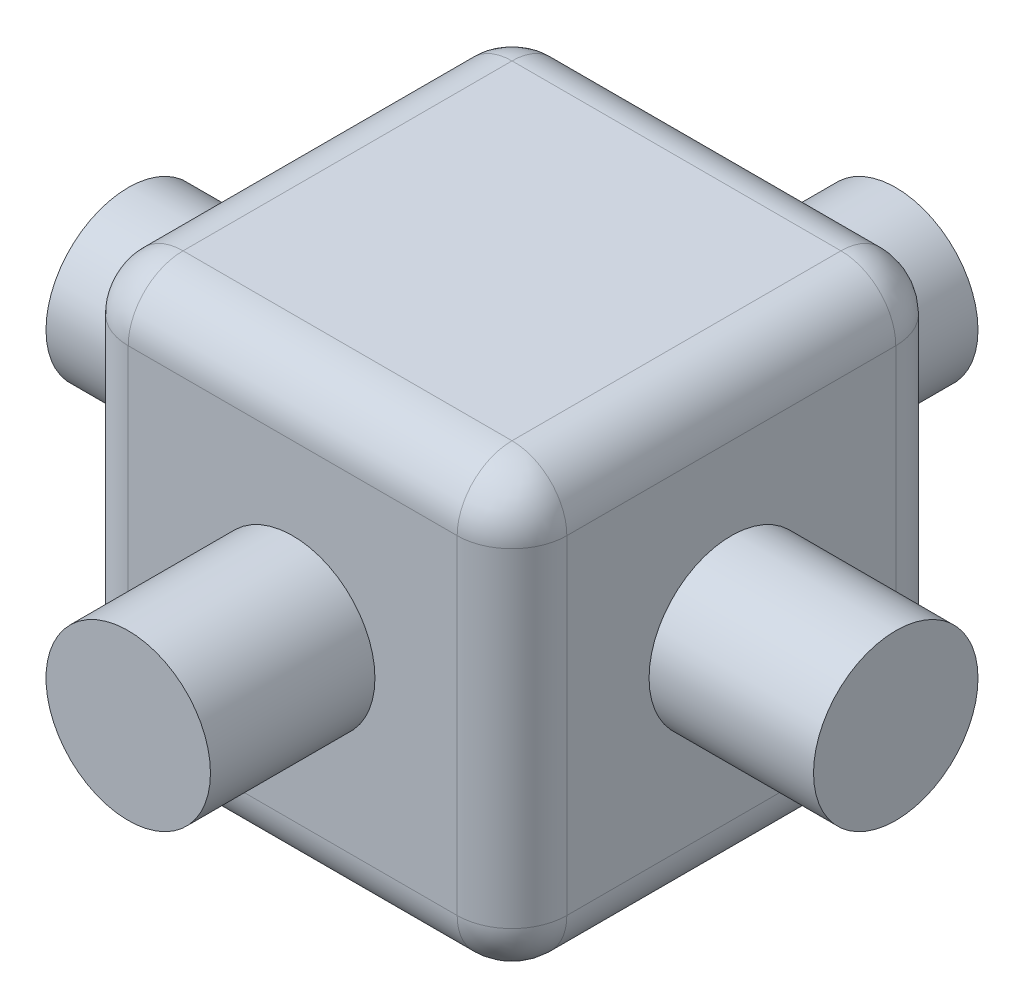
SolidWorks part; units mm, degrees
ref_plane "Front Plane" through (0, 0, 0) normal (0, 0, 1) x (1, 0, 0)
ref_plane "Top Plane" through (0, 0, 0) normal (0, 1, 0) x (1, 0, 0)
ref_plane "Right Plane" through (0, 0, 0) normal (1, 0, 0) x (0, 0, -1)
sketch "Sketch1" plane through (0, 0, 0) normal (0, 0, 1) x (1, 0, 0)
  circle A0 centre (0, 0) radius 0.75
  dimension "D1" = 1.5
extrude "Boss-Extrude1" add sketch "Sketch1" along normal mid plane 7
ref_axis "Axis1" through (0, -1.485, 0) along (0, 1, 0)
pattern_circular "CirPattern1" count 4 over 360 about axis through (0, -1.485, 0) along (0, 1, 0) of "Boss-Extrude1"
sketch "Sketch3" plane through (0, 0, 0) normal (0, 1, 0) x (1, 0, 0)
  line L0 (-2, -2) -> (-2, 2)
  line L1 (0.75, -0.75) -> (-0.75, -0.75)
  line L2 (0.75, -0.75) -> (0.75, 0.75)
  line L3 (0.75, 0.75) -> (-0.75, 0.75)
  line L4 (-0.75, -0.75) -> (-0.75, 0.75)
  line L5 (0.75, -0.75) -> (-0.75, 0.75) construction
  line L6 (0.75, 0.75) -> (-0.75, -0.75) construction
  line L7 (2, 2) -> (-2, 2)
  line L8 (2, -2) -> (2, 2)
  line L9 (2, -2) -> (-2, -2)
  point P0 (0, 0)
  dimension "D2" = 1.5
  dimension "D1" = 4
extrude "Boss-Extrude2" add sketch "Sketch3" along normal mid plane 4 contours L4 L1 L2 L3 | L9 L8 L7 L0 L1 L4 L3 L2
fillet "Fillet1" radius 0.5 12 edges at (2, 2, 0) (2, 0, -2) (0, 2, -2) (2, -2, 0) (0, -2, -2) (-2, 0, -2) (-2, 2, 0) (-2, -2, 0) (0, -2, 2) (2, 0, 2) (-2, 0, 2) (0, 2, 2)
